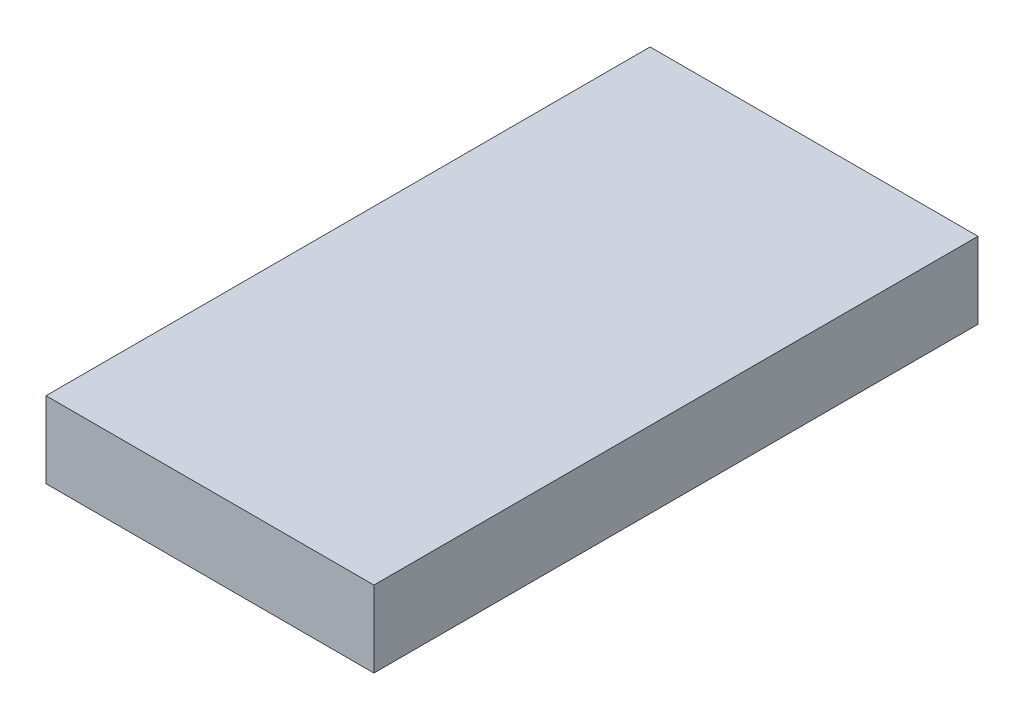
SolidWorks part; units mm, degrees
ref_plane "Front Plane" through (0, 0, 0) normal (0, 0, 1) x (1, 0, 0)
ref_plane "Top Plane" through (0, 0, 0) normal (0, 1, 0) x (1, 0, 0)
ref_plane "Right Plane" through (0, 0, 0) normal (1, 0, 0) x (0, 0, -1)
sketch "Sketch1" plane through (0, 0, 0) normal (0, 1, 0) x (1, 0, 0)
  line L1 (-28.5, 52.5) -> (28.5, 52.5)
  line L2 (-28.5, 52.5) -> (-28.5, -52.5)
  line L3 (-28.5, -52.5) -> (28.5, -52.5)
  line L4 (28.5, 52.5) -> (28.5, -52.5)
  line L5 (-28.5, 52.5) -> (28.5, -52.5) construction
  line L6 (-28.5, -52.5) -> (28.5, 52.5) construction
  point P0 (0, 0)
  dimension "D1" = 57
  dimension "D2" = 105
extrude "Boss-Extrude1" add sketch "Sketch1" along normal blind 13.25
